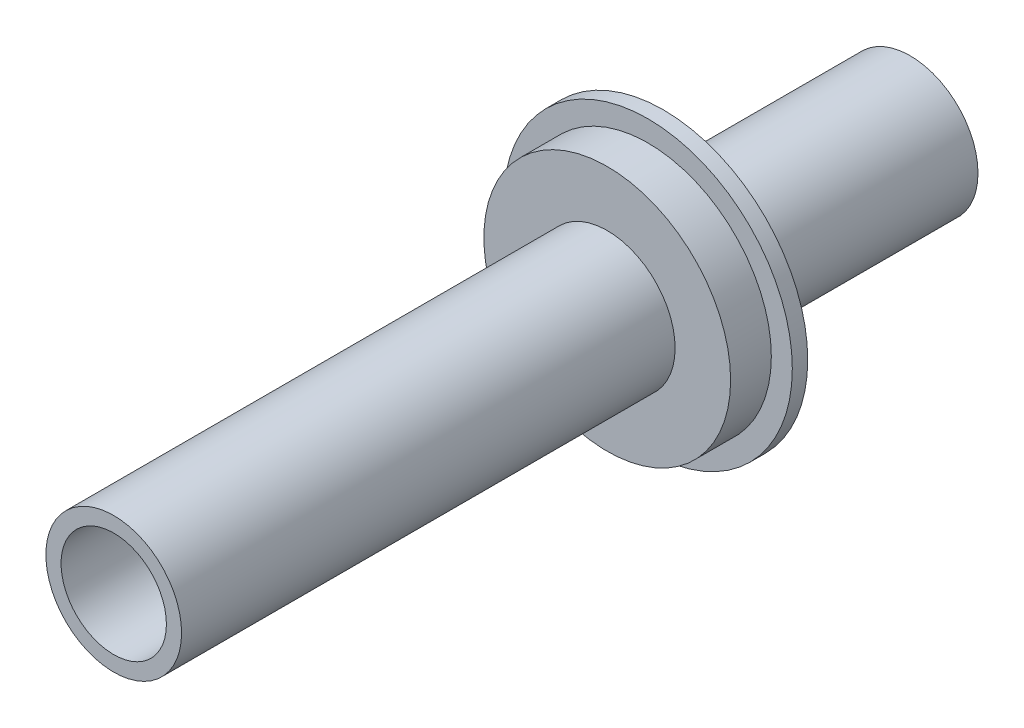
SolidWorks part; units mm, degrees
ref_plane "Front Plane" through (0, 0, 0) normal (0, 0, 1) x (1, 0, 0)
ref_plane "Top Plane" through (0, 0, 0) normal (0, 1, 0) x (1, 0, 0)
ref_plane "Right Plane" through (0, 0, 0) normal (1, 0, 0) x (0, 0, -1)
sketch "Sketch1" plane through (0, 0, 0) normal (0, 0, 1) x (1, 0, 0)
  circle A0 centre (0, 0) radius 13.97
extrude "Boss-Extrude2" add sketch "Sketch1" along normal blind 50.8
sketch "Sketch2" plane through (0, 0, 50.8) normal (0, 0, 1) x (1, 0, 0)
  circle A0 centre (0, 0) radius 29.718
extrude "Boss-Extrude3" add sketch "Sketch2" along normal blind 3.175
sketch "Sketch3" plane through (0, 0, 53.975) normal (0, 0, 1) x (1, 0, 0)
  circle A0 centre (0, 0) radius 25.4
extrude "Boss-Extrude4" add sketch "Sketch3" along normal blind 8.382
sketch "Sketch4" plane through (0, 0, 62.357) normal (0, 0, 1) x (1, 0, 0)
  circle A0 centre (0, 0) radius 13.97
extrude "Boss-Extrude5" add sketch "Sketch4" along normal blind 101.6
sketch "Sketch5" plane through (0, 0, 163.957) normal (0, 0, 1) x (1, 0, 0)
  circle A0 centre (0, 0) radius 10.8428
extrude "Cut-Extrude1" cut sketch "Sketch5" against normal up to surface (101.6 mm away) up to face at (13.97, 0, 62.357)
